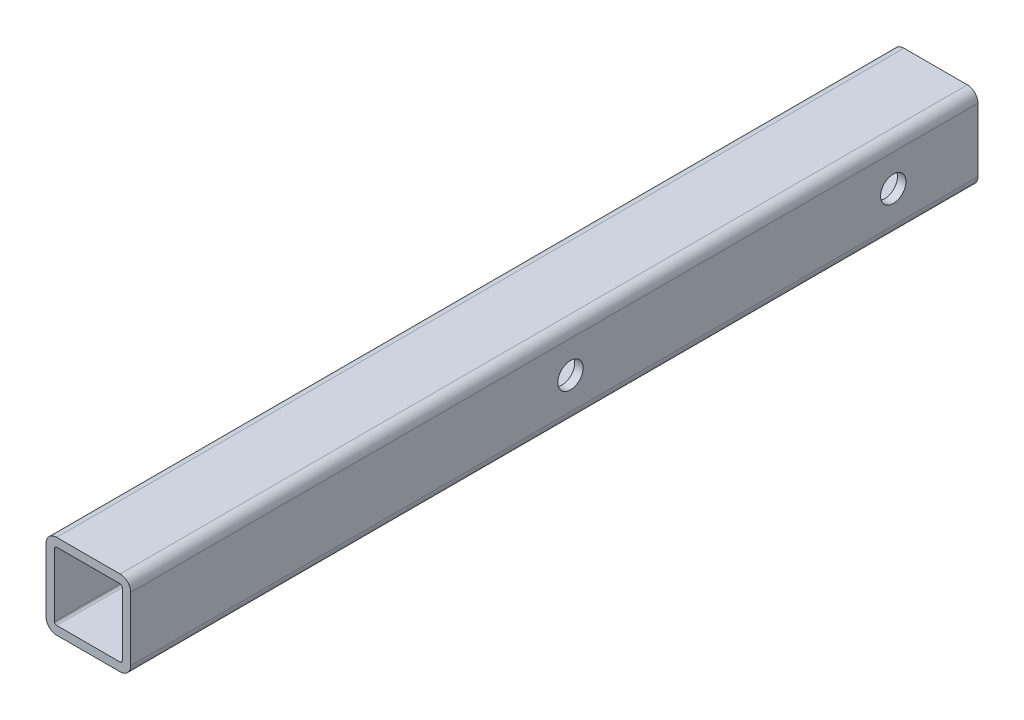
SolidWorks part; units mm, degrees
ref_plane "Front Plane" through (0, 0, 0) normal (0, 0, 1) x (1, 0, 0)
ref_plane "Top Plane" through (0, 0, 0) normal (0, 1, 0) x (1, 0, 0)
ref_plane "Right Plane" through (0, 0, 0) normal (1, 0, 0) x (0, 0, -1)
sketch "Sketch1" plane through (0, 0, 0) normal (0, 0, 1) x (1, 0, 0)
  line L1 (7.5, -10) -> (-7.5, -10)
  line L2 (10, -7.5) -> (10, 7.5)
  line L3 (7.5, 10) -> (-7.5, 10)
  line L4 (-10, -7.5) -> (-10, 7.5)
  line L5 (10, -10) -> (-10, 10) construction
  line L6 (10, 10) -> (-10, -10) construction
  arc A0 (-7.5, 10) -> (-10, 7.5) centre (-7.5, 7.5) ccw
  arc A1 (10, 7.5) -> (7.5, 10) centre (7.5, 7.5) ccw
  arc A2 (7.5, -10) -> (10, -7.5) centre (7.5, -7.5) ccw
  arc A3 (-7.5, -10) -> (-10, -7.5) centre (-7.5, -7.5) cw
  point P0 (0, 0)
  dimension "D2" = 2.5
  dimension "D1" = 20
extrude "Extrude-Thin1" add sketch "Sketch1" along normal mid plane 200 thin
sketch "Çizim1" plane through (10, 0, 0) normal (1, 0, 0) x (0, 0, -1)
  line L0 (100, -7.5) -> (100, 7.5) construction
  circle A0 centre (80, 0) radius 3
  circle A1 centre (3.8, 0) radius 3
  dimension "D1" = 20
  dimension "D2" = 76.2
extrude "Kes-Ekstrüzyon1" cut sketch "Çizim1" against normal blind 20.32
equation "\"D2@Sketch1\" = \"D5@Extrude-Thin1\" * 1.25"
